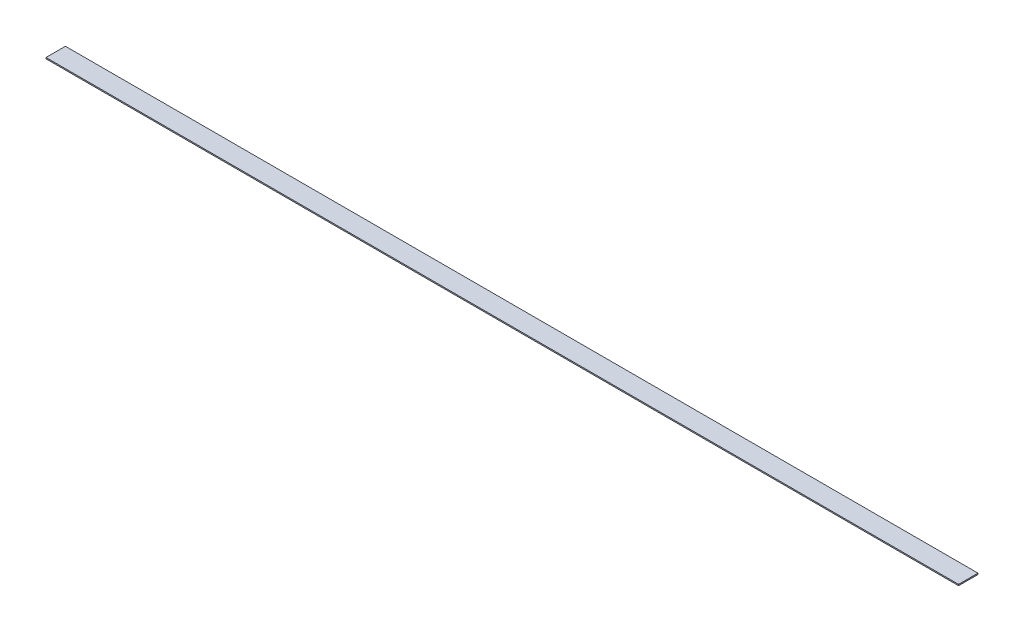
SolidWorks part; units mm, degrees
ref_plane "Front Plane" through (0, 0, 0) normal (0, 0, 1) x (1, 0, 0)
ref_plane "Top Plane" through (0, 0, 0) normal (0, 1, 0) x (1, 0, 0)
ref_plane "Right Plane" through (0, 0, 0) normal (1, 0, 0) x (0, 0, -1)
sketch "Sketch1" plane through (0, 0, 0) normal (0, 1, 0) x (1, 0, 0)
  line L1 (-596.9, 12.7) -> (596.9, 12.7)
  line L2 (-596.9, 12.7) -> (-596.9, -12.7)
  line L3 (-596.9, -12.7) -> (596.9, -12.7)
  line L4 (596.9, 12.7) -> (596.9, -12.7)
  line L5 (-596.9, 12.7) -> (596.9, -12.7) construction
  line L6 (-596.9, -12.7) -> (596.9, 12.7) construction
  point P0 (0, 0)
  dimension "D1" = 1193.8
  dimension "D2" = 25.4
extrude "Boss-Extrude1" add sketch "Sketch1" along normal blind 1.5875
